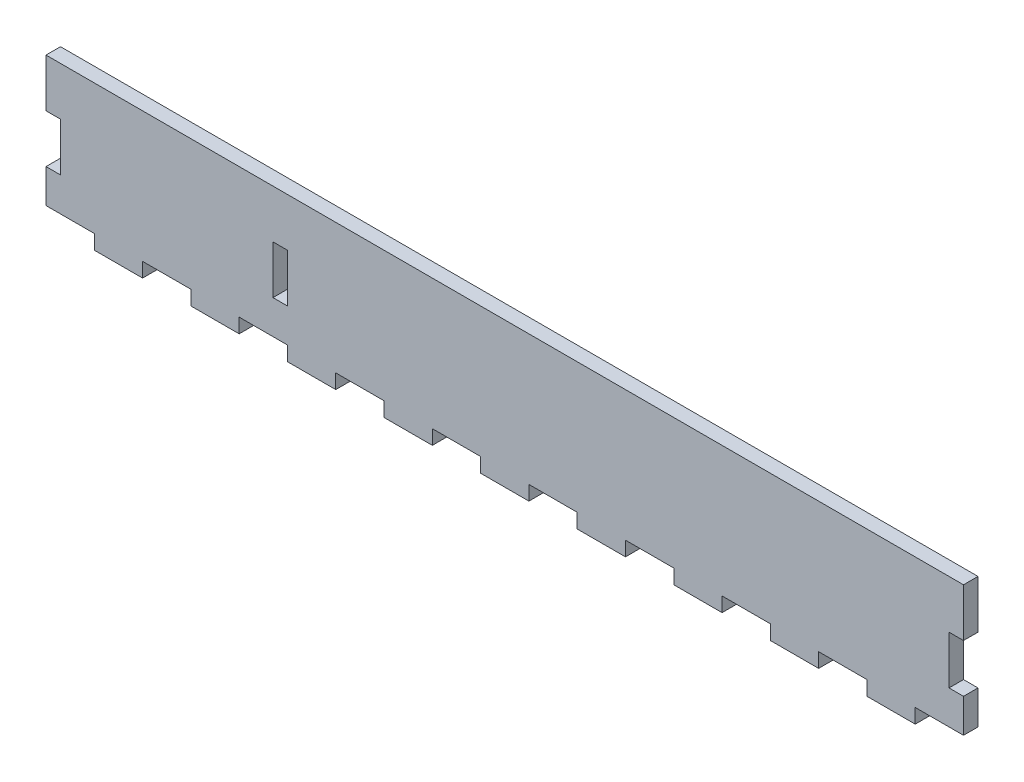
SolidWorks part; units mm, degrees
ref_plane "Front Plane" through (0, 0, 0) normal (0, 0, 1) x (1, 0, 0)
ref_plane "Top Plane" through (0, 0, 0) normal (0, 1, 0) x (1, 0, 0)
ref_plane "Right Plane" through (0, 0, 0) normal (1, 0, 0) x (0, 0, -1)
sketch "Sketch1" plane through (0, 0, 0) normal (0, 0, 1) x (1, 0, 0)
  line L0 (-114.5134, -81.4371) -> (-114.5134, -71.4371)
  line L1 (-14.5134, -71.4371) -> (265.4866, -71.4371)
  line L3 (-14.5134, -131.4371) -> (265.4866, -131.4371)
  line L4 (265.4866, -71.4371) -> (265.4866, -131.4371)
  line L5 (-14.5134, -131.4371) -> (-114.5134, -131.4371)
  line L8 (-114.5134, -131.4371) -> (-114.5134, -81.4371)
  line L9 (-114.5134, -71.4371) -> (-14.5134, -71.4371)
  dimension "D1" = 60
  dimension "D2" = 280
  dimension "D3" = 100
  dimension "D4" = 50
extrude "Boss-Extrude1" add sketch "Sketch1" along normal blind 6
sketch "Sketch2" plane through (0, 0, 6) normal (0, 0, 1) x (1, 0, 0)
  line L0 (-114.5134, -71.4371) -> (-114.5134, -131.4371) construction
  line L1 (-114.5134, -91.4371) -> (-108.5134, -91.4371)
  line L2 (-114.5134, -91.4371) -> (-114.5134, -111.4371)
  line L3 (-114.5134, -111.4371) -> (-108.5134, -111.4371)
  line L4 (-108.5134, -91.4371) -> (-108.5134, -111.4371)
  line L5 (265.4866, -71.4371) -> (-114.5134, -71.4371) construction
  dimension "D1" = 20
  dimension "D2" = 20
  dimension "D3" = 6
extrude "Cut-Extrude1" cut sketch "Sketch2" against normal blind 10
sketch "Sketch3" plane through (0, 0, 6) normal (0, 0, 1) x (1, 0, 0)
  line L0 (-108.5134, -91.4371) -> (-114.5134, -91.4371) construction
  line L1 (-20.5134, -91.4371) -> (-14.5134, -91.4371)
  line L2 (-20.5134, -91.4371) -> (-20.5134, -111.4371)
  line L3 (-20.5134, -111.4371) -> (-14.5134, -111.4371)
  line L4 (-14.5134, -91.4371) -> (-14.5134, -111.4371)
  line L5 (-114.5134, -111.4371) -> (-108.5134, -111.4371) construction
  line L7 (-114.5134, -111.4371) -> (-114.5134, -131.4371) construction
  dimension "D1" = 0
  dimension "D2" = 0
  dimension "D3" = 100
  dimension "D4" = 6
extrude "Cut-Extrude2" cut sketch "Sketch3" against normal blind 10
sketch "Sketch4" plane through (0, 0, 6) normal (0, 0, 1) x (1, 0, 0)
  line L0 (-114.5134, -131.4371) -> (265.4866, -131.4371) construction
  line L1 (-114.5134, -131.4371) -> (-94.5134, -131.4371)
  line L2 (-114.5134, -131.4371) -> (-114.5134, -125.4371)
  line L3 (-114.5134, -125.4371) -> (-94.5134, -125.4371)
  line L4 (-94.5134, -131.4371) -> (-94.5134, -125.4371)
  line L5 (-114.5134, -111.4371) -> (-114.5134, -131.4371) construction
  dimension "D1" = 6
  dimension "D2" = 0
  dimension "D3" = 20
extrude "Cut-Extrude3" cut sketch "Sketch4" against normal blind 10
pattern_linear "LPattern1" count 10 spacing 40 along (1, 0, 0) of "Cut-Extrude3"
sketch "Sketch5" plane through (0, 0, 6) normal (0, 0, 1) x (1, 0, 0)
  line L1 (265.4866, -91.4371) -> (259.4866, -91.4371)
  line L2 (265.4866, -91.4371) -> (265.4866, -111.4371)
  line L3 (265.4866, -111.4371) -> (259.4866, -111.4371)
  line L4 (259.4866, -91.4371) -> (259.4866, -111.4371)
  line L6 (265.4866, -71.4371) -> (-114.5134, -71.4371) construction
  dimension "D1" = 6
  dimension "D2" = 20
  dimension "D3" = 20
extrude "Cut-Extrude4" cut sketch "Sketch5" against normal blind 10
